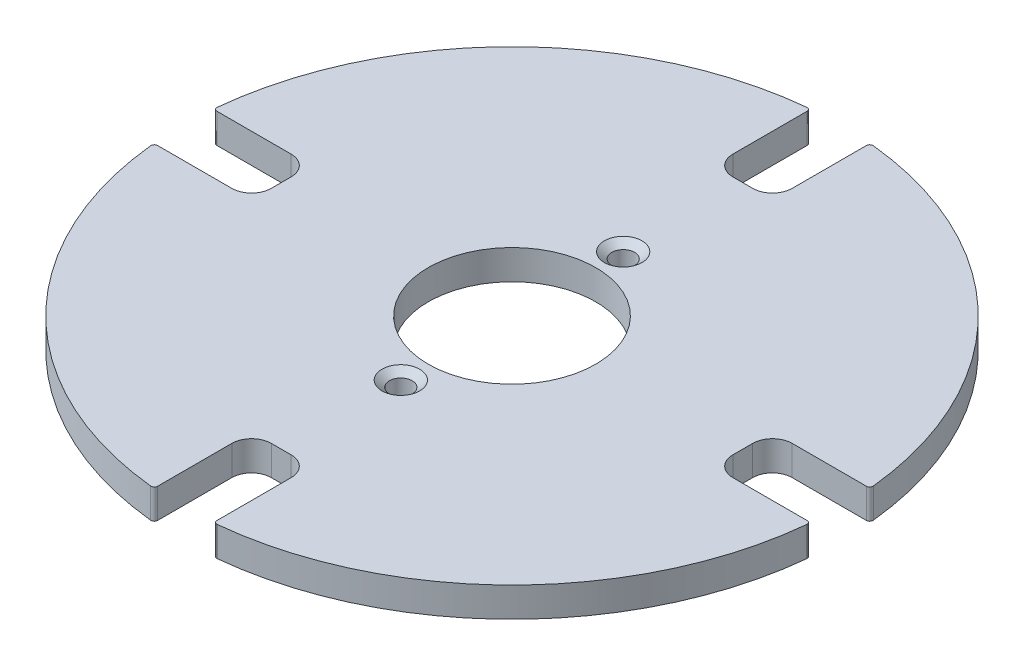
SolidWorks part; units mm, degrees
ref_plane "Front Plane" through (0, 0, 0) normal (0, 0, 1) x (1, 0, 0)
ref_plane "Top Plane" through (0, 0, 0) normal (0, 1, 0) x (1, 0, 0)
ref_plane "Right Plane" through (0, 0, 0) normal (1, 0, 0) x (0, 0, -1)
sketch "Sketch3" plane through (0, 0, 0) normal (0, 1, 0) x (1, 0, 0)
  circle A0 centre (0, 0) radius 50
  circle A1 centre (0, 0) radius 12.7
  circle A2 centre (0, 0) radius 16.8627 construction
  dimension "D1" = 25.4
extrude "Boss-Extrude4" add sketch "Sketch3" along normal blind 4.5
sketch "Sketch6" plane through (0, 0, 0) normal (0, 1, 0) x (1, 0, 0)
  line L0 (0, 0) -> (89.4122, 0) construction
  line L1 (-38, -4.5) -> (-65, -4.5)
  line L2 (-35, -1.5) -> (-35, 1.5)
  line L3 (-38, 4.5) -> (-65, 4.5)
  line L4 (-65, -4.5) -> (-65, 4.5)
  line L5 (-35, -4.5) -> (-65, 4.5) construction
  line L6 (-35, 4.5) -> (-65, -4.5) construction
  line L7 (0, 0) -> (0, -68.3888) construction
  line L8 (0, 0) -> (0, 80.8497) construction
  line L9 (-4.5, 38) -> (-4.5, 65)
  line L10 (-1.5, 35) -> (1.5, 35)
  line L11 (4.5, 38) -> (4.5, 65)
  line L12 (-4.5, 65) -> (4.5, 65)
  line L13 (-4.5, 35) -> (4.5, 65) construction
  line L14 (4.5, 35) -> (-4.5, 65) construction
  line L15 (38, 4.5) -> (65, 4.5)
  line L16 (35, 1.5) -> (35, -1.5)
  line L17 (38, -4.5) -> (65, -4.5)
  line L18 (65, 4.5) -> (65, -4.5)
  line L19 (35, 4.5) -> (65, -4.5) construction
  line L20 (35, -4.5) -> (65, 4.5) construction
  line L21 (4.5, -38) -> (4.5, -65)
  line L22 (1.5, -35) -> (-1.5, -35)
  line L23 (-4.5, -38) -> (-4.5, -65)
  line L24 (0, 0) -> (-101.315, 0) construction
  line L25 (4.5, -65) -> (-4.5, -65)
  line L26 (4.5, -35) -> (-4.5, -65) construction
  line L27 (-4.5, -35) -> (4.5, -65) construction
  circle A0 centre (0, 0) radius 50 construction
  arc A1 (-38, 4.5) -> (-35, 1.5) centre (-38, 1.5) cw
  arc A2 (-38, -4.5) -> (-35, -1.5) centre (-38, -1.5) ccw
  arc A3 (4.5, 38) -> (1.5, 35) centre (1.5, 38) cw
  arc A4 (-4.5, 38) -> (-1.5, 35) centre (-1.5, 38) ccw
  arc A5 (38, -4.5) -> (35, -1.5) centre (38, -1.5) cw
  arc A6 (38, 4.5) -> (35, 1.5) centre (38, 1.5) ccw
  arc A7 (-4.5, -38) -> (-1.5, -35) centre (-1.5, -38) cw
  arc A8 (4.5, -38) -> (1.5, -35) centre (1.5, -38) ccw
  point P0 (-50, 0)
  point P21 (0, 50)
  point P22 (0, 0)
  point P33 (50, 0)
  point P41 (0, 5.6)
  point P42 (0, 0)
  point P46 (0, -50)
  point P47 (2.6408, 2.6408)
  point P51 (-2.6408, -2.6408)
  point P54 (0, 0.5)
  point P61 (0, 0)
  dimension "D3" = 3
  dimension "D4" = 3
  dimension "D1" = 9
  dimension "D2" = 30
  dimension "D5" = 4
extrude "Cut-Extrude18" cut sketch "Sketch6" along normal blind 10
sketch "Sketch7" plane through (0, 0, 0) normal (0, 1, 0) x (1, 0, 0)
  line L0 (0, 0) -> (92.619, 0) construction
  line L1 (0, 0) -> (-95.6074, 0) construction
  line L2 (0, 0) -> (0, -61.0615) construction
  line L3 (0, 0) -> (0, 63.4251) construction
  circle A4 centre (0, 0) radius 50
  dimension "D1" = 100
fillet "Fillet2" radius 0.5 8 edges at (-49.7971, 2.25, 4.5) (-49.7971, 2.25, -4.5) (4.5, 2.25, -49.7971) (-4.5, 2.25, -49.7971) (49.7971, 2.25, -4.5) (49.7971, 2.25, 4.5) (4.5, 2.25, 49.7971) (-4.5, 2.25, 49.7971)
hole_wizard "CSK for #4 Flat Head Machine Screw (100)1" positions "Sketch9" profile "Sketch8" countersink size "#4" standard "ANSI Inch" end condition through all
sketch "Sketch9" plane through (0, 4.5, 0) normal (0, 1, 0) x (1, 0, 0)
  line L0 (0, 0) -> (0, -61.0615) construction
  circle A0 centre (0, 0) radius 16.8627 construction
  point P0 (0, -16.8627)
  point P6 (0, 16.8627)
sketch "Sketch8" plane through (0, 4.5, 16.8627) normal (1, 0, 0) x (0, 0, 1)
  line L0 (0, 0) -> (0, 4.5)
  line L1 (0, 4.5) -> (1.7272, 4.5)
  line L2 (1.7272, 4.5) -> (1.7272, 0.9484)
  line L3 (1.7272, 0.9484) -> (2.8575, 0)
  line L5 (2.8575, 0) -> (0, 0)
  line L6 (-1.7272, 0.9484) -> (-2.8575, 0) construction
  line L11 (0, -6.35) -> (0, 107.95) construction
  dimension "Thru Hole Dia." = 3.4544
  dimension "Thru Hole Depth" = 4.5
  dimension "Near C'Sink Dia." = 5.715
  dimension "Near C'Sink Angle" = 100
